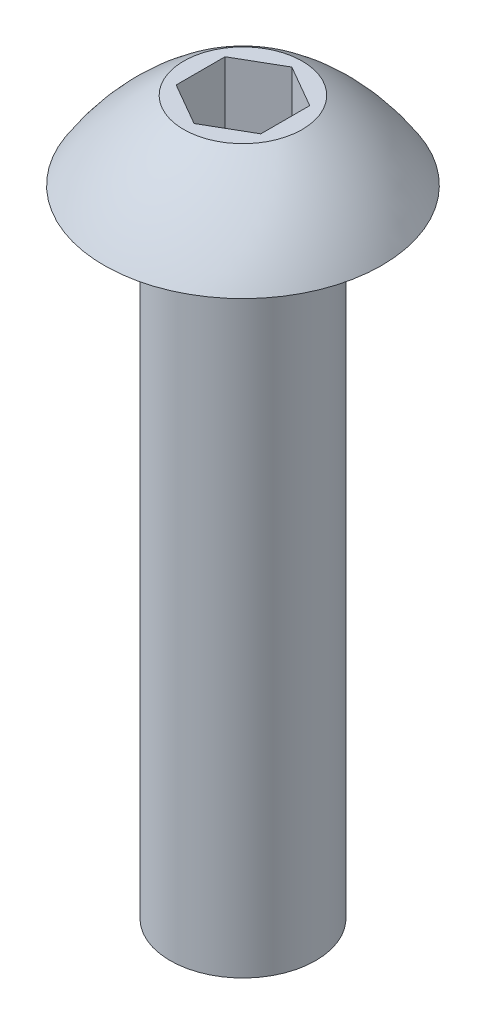
SolidWorks part; units mm, degrees
material "AISI Type 316L stainless steel"
ref_plane "Front Plane" through (0, 0, 0) normal (0, 0, 1) x (1, 0, 0)
ref_plane "Top Plane" through (0, 0, 0) normal (0, 1, 0) x (1, 0, 0)
ref_plane "Right Plane" through (0, 0, 0) normal (1, 0, 0) x (0, 0, -1)
sketch "Sketch1" plane through (0, 0, 0) normal (0, 0, 1) x (1, 0, 0)
  line L0 (-1.0922, 0) -> (-2.0828, 0)
  line L1 (-1.0922, 0) -> (-1.0922, -9.525)
  line L2 (0, -9.525) -> (0, 1.1684)
  line L3 (0, 1.1684) -> (-0.889, 1.1684)
  line L4 (-1.0922, -9.525) -> (0, -9.525)
  arc A0 (-2.0828, 0) -> (-0.889, 1.1684) centre (0.9356, -1.8899) cw
  dimension "D1" = 9.525
  dimension "D2" = 1.1684
  dimension "D3" = 2.0828
  dimension "D4" = 1.0922
  dimension "D5" = 0.889
revolve "Revolve1" add sketch "Sketch1" angle 360 about L2
sketch "Sketch2" plane through (0, 1.1684, 0) normal (0, 1, 0) x (1, 0, 0)
  line L0 (0, 0) -> (0, 0.7332) construction
  line L1 (-0.635, 0.3666) -> (-0.635, -0.3666)
  line L2 (-0.635, -0.3666) -> (0, -0.7332)
  line L3 (0, -0.7332) -> (0.635, -0.3666)
  line L4 (0.635, -0.3666) -> (0.635, 0.3666)
  line L5 (0.635, 0.3666) -> (0, 0.7332)
  line L6 (0, 0.7332) -> (-0.635, 0.3666)
  circle A0 centre (0, 0) radius 0.635 construction
  dimension "D1" = 1.27
extrude "Cut-Extrude1" cut sketch "Sketch2" against normal blind 1.27
